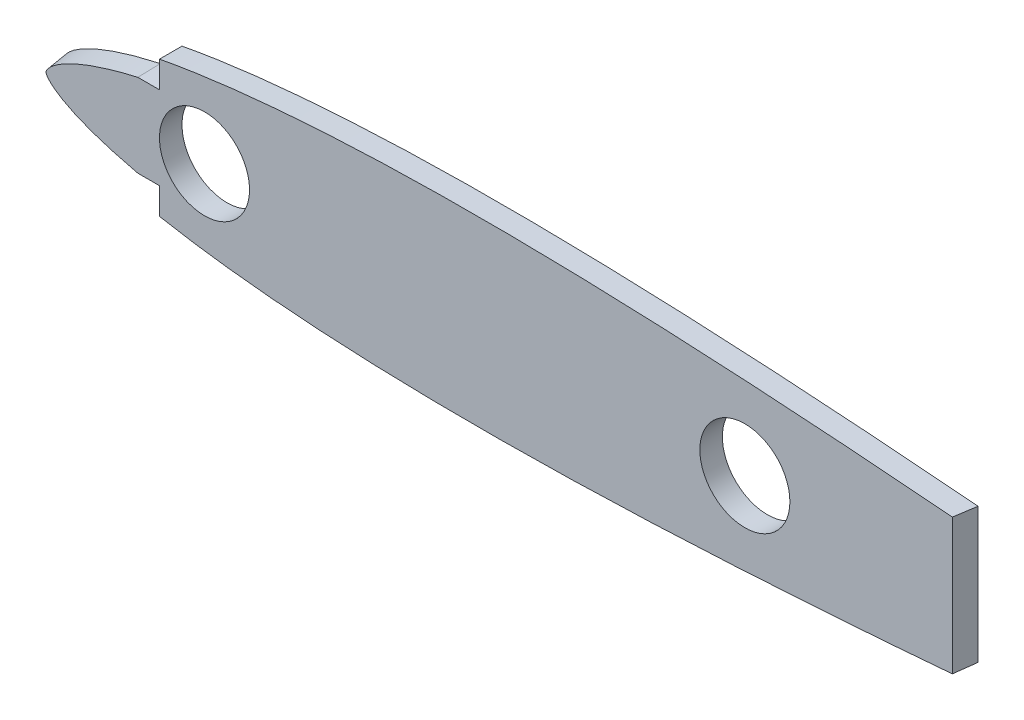
SolidWorks part; units mm, degrees
material "Balsa"
ref_plane "Front Plane" through (0, 0, 0) normal (0, 0, 1) x (1, 0, 0)
ref_plane "Top Plane" through (0, 0, 0) normal (0, 1, 0) x (1, 0, 0)
ref_plane "Right Plane" through (0, 0, 0) normal (1, 0, 0) x (0, 0, -1)
curve "Curve6"
  spline degree 3 poles (214.2507, -0.3619, 0) (214.2507, 0.3619, 0) (213.529, 0.2735, 0) (212.6145, 0.5309, 0) (210.9374, 0.6901, 0) (208.6782, 1.0315, 0) (205.7679, 1.4126, 0) (202.2583, 1.8823, 0) (198.1585, 2.4132, 0) (193.4982, 3.0043, 0) (188.3046, 3.6452, 0) (182.6103, 4.3273, 0) (176.4501, 5.042, 0) (169.8621, 5.7798, 0) (162.8869, 6.5315, 0) (155.5675, 7.2878, 0) (147.9491, 8.039, 0) (140.0787, 8.7745, 0) (132.0046, 9.4847, 0) (123.7769, 10.1577, 0) (115.4459, 10.7824, 0) (107.0633, 11.3474, 0) (98.6805, 11.8408, 0) (90.3493, 12.2502, 0) (82.1211, 12.5645, 0) (74.0464, 12.7737, 0) (66.175, 12.8673, 0) (58.5554, 12.8381, 0) (51.2345, 12.6804, 0) (44.2574, 12.3902, 0) (37.667, 11.9666, 0) (31.5038, 11.4111, 0) (25.8056, 10.7279, 0) (20.6071, 9.9229, 0) (15.9397, 9.0044, 0) (11.8309, 7.9828, 0) (8.304, 6.8681, 0) (5.3769, 5.6708, 0) (3.0589, 4.3988, 0) (1.3536, 3.0497, 0) (0.2614, 1.5908, 0) (-0.1218, 0, 0) (0.2614, -1.5908, 0) (1.3536, -3.0497, 0) (3.0589, -4.3988, 0) (5.3769, -5.6708, 0) (8.304, -6.8681, 0) (11.8309, -7.9828, 0) (15.9397, -9.0044, 0) (20.6071, -9.9229, 0) (25.8056, -10.7279, 0) (31.5038, -11.4111, 0) (37.667, -11.9666, 0) (44.2574, -12.3902, 0) (51.2345, -12.6804, 0) (58.5554, -12.8381, 0) (66.175, -12.8673, 0) (74.0464, -12.7737, 0) (82.1211, -12.5645, 0) (90.3493, -12.2502, 0) (98.6805, -11.8408, 0) (107.0633, -11.3474, 0) (115.4459, -10.7824, 0) (123.7769, -10.1577, 0) (132.0046, -9.4847, 0) (140.0787, -8.7745, 0) (147.9491, -8.039, 0) (155.5675, -7.2878, 0) (162.8869, -6.5315, 0) (169.8621, -5.7798, 0) (176.4501, -5.042, 0) (182.6103, -4.3273, 0) (188.3046, -3.6452, 0) (193.4982, -3.0043, 0) (198.1585, -2.4132, 0) (202.2583, -1.8823, 0) (205.7679, -1.4126, 0) (208.6782, -1.0315, 0) (210.9374, -0.6901, 0) (212.6145, -0.5309, 0) (213.529, -0.2735, 0) (214.2507, -0.3619, 0) (214.2507, 0.3619, 0) (213.529, 0.2735, 0) knots -0.004279 -0.001997 -0.001234 0 0.000762 0.003045 0.006832 0.012101 0.018818 0.026939 0.036415 0.047185 0.05918 0.072328 0.086544 0.101741 0.117823 0.134691 0.15224 0.170361 0.188941 0.207865 0.227016 0.246276 0.265525 0.284645 0.30352 0.322035 0.340078 0.357543 0.374325 0.39033 0.405464 0.419644 0.432793 0.444844 0.455738 0.465429 0.473886 0.481102 0.487102 0.491975 0.495931 0.499383 0.502835 0.50679 0.511664 0.517664 0.524879 0.533337 0.543028 0.553922 0.565972 0.579122 0.593302 0.608436 0.62444 0.641223 0.658687 0.676731 0.695245 0.714121 0.733241 0.75249 0.77175 0.7909 0.809825 0.828404 0.846525 0.864074 0.880942 0.897025 0.912222 0.926438 0.939585 0.951581 0.962351 0.971826 0.979948 0.986664 0.991933 0.995721 0.998003 0.998766 1 1.000762 1.003045 1.006832 periodic
sketch "Sketch1" plane through (0, 0, 0) normal (0, 0, 1) x (1, 0, 0)
  spline S0 degree 3 poles (214.2507, -0.3619) (214.2507, 0.3619) (213.529, 0.2735) (212.6145, 0.5309) (210.9374, 0.6901) (208.6782, 1.0315) (205.7679, 1.4126) (202.2583, 1.8823) (198.1585, 2.4132) (193.4982, 3.0043) (188.3046, 3.6452) (182.6103, 4.3273) (176.4501, 5.042) (169.8621, 5.7798) (162.8869, 6.5315) (155.5675, 7.2878) (147.9491, 8.039) (140.0787, 8.7745) (132.0046, 9.4847) (123.7769, 10.1577) (115.4459, 10.7824) (107.0633, 11.3474) (98.6805, 11.8408) (90.3493, 12.2502) (82.1211, 12.5645) (74.0464, 12.7737) (66.175, 12.8673) (58.5554, 12.8381) (51.2345, 12.6804) (44.2574, 12.3902) (37.667, 11.9666) (31.5038, 11.4111) (25.8056, 10.7279) (20.6071, 9.9229) (15.9397, 9.0044) (11.8309, 7.9828) (8.304, 6.8681) (5.3769, 5.6708) (3.0589, 4.3988) (1.3536, 3.0497) (0.2614, 1.5908) (-0.1218, 0) (0.2614, -1.5908) (1.3536, -3.0497) (3.0589, -4.3988) (5.3769, -5.6708) (8.304, -6.8681) (11.8309, -7.9828) (15.9397, -9.0044) (20.6071, -9.9229) (25.8056, -10.7279) (31.5038, -11.4111) (37.667, -11.9666) (44.2574, -12.3902) (51.2345, -12.6804) (58.5554, -12.8381) (66.175, -12.8673) (74.0464, -12.7737) (82.1211, -12.5645) (90.3493, -12.2502) (98.6805, -11.8408) (107.0633, -11.3474) (115.4459, -10.7824) (123.7769, -10.1577) (132.0046, -9.4847) (140.0787, -8.7745) (147.9491, -8.039) (155.5675, -7.2878) (162.8869, -6.5315) (169.8621, -5.7798) (176.4501, -5.042) (182.6103, -4.3273) (188.3046, -3.6452) (193.4982, -3.0043) (198.1585, -2.4132) (202.2583, -1.8823) (205.7679, -1.4126) (208.6782, -1.0315) (210.9374, -0.6901) (212.6145, -0.5309) (213.529, -0.2735) (214.2507, -0.3619) (214.2507, 0.3619) (213.529, 0.2735) knots -0.004279 -0.001997 -0.001234 0 0.000762 0.003045 0.006832 0.012101 0.018818 0.026939 0.036415 0.047185 0.05918 0.072328 0.086544 0.101741 0.117823 0.134691 0.15224 0.170361 0.188941 0.207865 0.227016 0.246276 0.265525 0.284645 0.30352 0.322035 0.340078 0.357543 0.374325 0.39033 0.405464 0.419644 0.432793 0.444844 0.455738 0.465429 0.473886 0.481102 0.487102 0.491975 0.495931 0.499383 0.502835 0.50679 0.511664 0.517664 0.524879 0.533337 0.543028 0.553922 0.565972 0.579122 0.593302 0.608436 0.62444 0.641223 0.658687 0.676731 0.695245 0.714121 0.733241 0.75249 0.77175 0.7909 0.809825 0.828404 0.846525 0.864074 0.880942 0.897025 0.912222 0.926438 0.939585 0.951581 0.962351 0.971826 0.979948 0.986664 0.991933 0.995721 0.998003 0.998766 1 1.000762 1.003045 1.006832 only from (214.122, 0.2698) to (214.122, 0.2698) construction
  spline S1 degree 3 poles (214.2507, -0.3619) (214.2507, 0.3619) (213.529, 0.2735) (212.6145, 0.5309) (210.9374, 0.6901) (208.6782, 1.0315) (205.7679, 1.4126) (202.2583, 1.8823) (198.1585, 2.4132) (193.4982, 3.0043) (188.3046, 3.6452) (182.6103, 4.3273) (176.4501, 5.042) (169.8621, 5.7798) (162.8869, 6.5315) (155.5675, 7.2878) (147.9491, 8.039) (140.0787, 8.7745) (132.0046, 9.4847) (123.7769, 10.1577) (115.4459, 10.7824) (107.0633, 11.3474) (98.6805, 11.8408) (90.3493, 12.2502) (82.1211, 12.5645) (74.0464, 12.7737) (66.175, 12.8673) (58.5554, 12.8381) (51.2345, 12.6804) (44.2574, 12.3902) (37.667, 11.9666) (31.5038, 11.4111) (25.8056, 10.7279) (20.6071, 9.9229) (15.9397, 9.0044) (11.8309, 7.9828) (8.304, 6.8681) (5.3769, 5.6708) (3.0589, 4.3988) (1.3536, 3.0497) (0.2614, 1.5908) (-0.1218, 0) (0.2614, -1.5908) (1.3536, -3.0497) (3.0589, -4.3988) (5.3769, -5.6708) (8.304, -6.8681) (11.8309, -7.9828) (15.9397, -9.0044) (20.6071, -9.9229) (25.8056, -10.7279) (31.5038, -11.4111) (37.667, -11.9666) (44.2574, -12.3902) (51.2345, -12.6804) (58.5554, -12.8381) (66.175, -12.8673) (74.0464, -12.7737) (82.1211, -12.5645) (90.3493, -12.2502) (98.6805, -11.8408) (107.0633, -11.3474) (115.4459, -10.7824) (123.7769, -10.1577) (132.0046, -9.4847) (140.0787, -8.7745) (147.9491, -8.039) (155.5675, -7.2878) (162.8869, -6.5315) (169.8621, -5.7798) (176.4501, -5.042) (182.6103, -4.3273) (188.3046, -3.6452) (193.4982, -3.0043) (198.1585, -2.4132) (202.2583, -1.8823) (205.7679, -1.4126) (208.6782, -1.0315) (210.9374, -0.6901) (212.6145, -0.5309) (213.529, -0.2735) (214.2507, -0.3619) (214.2507, 0.3619) (213.529, 0.2735) knots -0.004279 -0.001997 -0.001234 0 0.000762 0.003045 0.006832 0.012101 0.018818 0.026939 0.036415 0.047185 0.05918 0.072328 0.086544 0.101741 0.117823 0.134691 0.15224 0.170361 0.188941 0.207865 0.227016 0.246276 0.265525 0.284645 0.30352 0.322035 0.340078 0.357543 0.374325 0.39033 0.405464 0.419644 0.432793 0.444844 0.455738 0.465429 0.473886 0.481102 0.487102 0.491975 0.495931 0.499383 0.502835 0.50679 0.511664 0.517664 0.524879 0.533337 0.543028 0.553922 0.565972 0.579122 0.593302 0.608436 0.62444 0.641223 0.658687 0.676731 0.695245 0.714121 0.733241 0.75249 0.77175 0.7909 0.809825 0.828404 0.846525 0.864074 0.880942 0.897025 0.912222 0.926438 0.939585 0.951581 0.962351 0.971826 0.979948 0.986664 0.991933 0.995721 0.998003 0.998766 1 1.000762 1.003045 1.006832 only from (214.122, 0.2698) to (214.122, 0.2698)
extrude "Boss-Extrude1" add sketch "Sketch1" along normal blind 3.175
sketch "Sketch2" plane through (0, 0, 3.175) normal (0, 0, 1) x (1, 0, 0)
  circle A0 centre (25.4, 0) radius 6.35
  circle A1 centre (101.6, 0) radius 6.35
  dimension "D1" = 12.7
  dimension "D2" = 12.7
  dimension "D3" = 0
  dimension "D4" = 0
  dimension "D5" = 25.4
  dimension "D6" = 101.6
extrude "Cut-Extrude1" cut sketch "Sketch2" against normal through all
sketch "Sketch4" plane through (0, 0, 0) normal (0, 1, 0) x (1, 0, 0)
  line L2 (131.3014, 0) -> (130.8547, -3.175)
  line L4 (214.2185, 0) -> (0, 0) construction
  line L5 (214.2185, 0) -> (131.3014, 0)
  line L6 (214.2185, -3.175) -> (214.2185, 0) construction
  line L7 (214.2185, -3.175) -> (214.2185, 0)
  line L11 (130.8547, -3.175) -> (214.2185, -3.175)
extrude "Cut-Extrude2" cut sketch "Sketch4" against normal through all both and the other way through all contours L5 L2 L11 L7
sketch "Sketch5" plane through (0, 0, 0) normal (0, 0, -1) x (-1, 0, 0)
  line L0 (-19.05, -9.6949) -> (-19.05, -5.9522)
  line L1 (-19.05, -9.6949) -> (-19.05, -5.9522)
  line L2 (-16.002, -5.9522) -> (-19.05, -5.9522)
  line L3 (-16.002, -5.9522) -> (-19.05, -5.9522)
  line L4 (-19.05, 5.9522) -> (-19.05, 9.6949)
  line L5 (-19.05, 5.9522) -> (-19.05, 9.6949)
  line L6 (-19.05, 5.9522) -> (-16.002, 5.9522)
  line L7 (-19.05, 5.9522) -> (-16.002, 5.9522)
  line L8 (-19.05, 9.6949) -> (-19.05, 12.3776)
  line L9 (-19.05, 12.3776) -> (3.9372, 8.6357)
  line L10 (3.9372, 8.6357) -> (2.5117, -11.7446)
  line L11 (2.5117, -11.7446) -> (-19.05, -12.3014)
  line L12 (-19.05, -12.3014) -> (-19.05, -9.6949)
  spline S0 degree 3 poles (1979.4926, 138.2298) (-139.8627, -22.8717) (-64.1253, 18.5865) (-12.6489, 5.1346) (-11.5484, 4.8257) (-10.4651, 4.4981) (-9.3996, 4.1488) (-8.3537, 3.7753) (-7.5049, 3.4422) (-6.8429, 3.1616) (-6.1948, 2.871) (-5.4147, 2.488) (-4.6839, 2.0746) (-4.1514, 1.7348) (-3.7822, 1.4766) (-3.4495, 1.2179) (-3.1565, 0.9593) (-2.9074, 0.7021) (-2.7169, 0.4734) (-2.62, 0.3293) (-2.5683, 0.2322) (-2.5397, 0.1664) (-2.5186, 0.105) (-2.5054, 0.0553) (-2.4997, 0.023) (-2.4987, 0) (-2.4997, -0.023) (-2.5054, -0.0553) (-2.5186, -0.105) (-2.5397, -0.1664) (-2.5683, -0.2322) (-2.62, -0.3293) (-2.7169, -0.4734) (-2.9074, -0.7021) (-3.1565, -0.9593) (-3.4496, -1.2179) (-3.7821, -1.4766) (-4.1514, -1.7348) (-4.6837, -2.0745) (-5.4148, -2.4881) (-6.1948, -2.871) (-6.8429, -3.1616) (-7.5049, -3.4422) (-8.3537, -3.7753) (-9.3996, -4.1488) (-10.4651, -4.4981) (-11.5484, -4.8257) (-12.649, -5.1346) (-63.4171, -18.4015) (-138.5465, 21.5522) (1981.2096, -108.9254) knots -4.215654 -4.215654 -4.215654 -4.215654 0.0625 0.09375 0.125 0.15625 0.1875 0.21875 0.25 0.265625 0.28125 0.3125 0.34375 0.359375 0.375 0.390625 0.40625 0.421875 0.4375 0.453125 0.460938 0.46875 0.476562 0.484375 0.492188 0.5 0.507812 0.515625 0.523438 0.53125 0.539062 0.546875 0.5625 0.578125 0.59375 0.609375 0.625 0.640625 0.65625 0.6875 0.71875 0.734375 0.75 0.78125 0.8125 0.84375 0.875 0.90625 0.9375 5.15664 5.15664 5.15664 5.15664 only from (-16.002, 5.9522) to (-16.002, -5.9522)
  spline S1 degree 3 poles (-16.002, 5.9522) (-15.2548, 5.7866) (-14.1313, 5.522) (-12.6489, 5.1346) (-11.5484, 4.8257) (-10.4651, 4.4981) (-9.3996, 4.1488) (-8.3537, 3.7753) (-7.5049, 3.4422) (-6.8429, 3.1616) (-6.1948, 2.871) (-5.4147, 2.488) (-4.6839, 2.0746) (-4.1514, 1.7348) (-3.7822, 1.4766) (-3.4495, 1.2179) (-3.1565, 0.9593) (-2.9074, 0.7021) (-2.7169, 0.4734) (-2.62, 0.3293) (-2.5683, 0.2322) (-2.5397, 0.1664) (-2.5186, 0.105) (-2.5054, 0.0553) (-2.4997, 0.023) (-2.4987, 0) (-2.4997, -0.023) (-2.5054, -0.0553) (-2.5186, -0.105) (-2.5397, -0.1664) (-2.5683, -0.2322) (-2.62, -0.3293) (-2.7169, -0.4734) (-2.9074, -0.7021) (-3.1565, -0.9593) (-3.4496, -1.2179) (-3.7821, -1.4766) (-4.1514, -1.7348) (-4.6837, -2.0745) (-5.4148, -2.4881) (-6.1948, -2.871) (-6.8429, -3.1616) (-7.5049, -3.4422) (-8.3537, -3.7753) (-9.3996, -4.1488) (-10.4651, -4.4981) (-11.5484, -4.8257) (-12.649, -5.1346) (-14.1311, -5.5219) (-15.2548, -5.7866) (-16.002, -5.9522) knots 0 0 0 0 0.0625 0.09375 0.125 0.15625 0.1875 0.21875 0.25 0.265625 0.28125 0.3125 0.34375 0.359375 0.375 0.390625 0.40625 0.421875 0.4375 0.453125 0.460938 0.46875 0.476562 0.484375 0.492188 0.5 0.507812 0.515625 0.523438 0.53125 0.539062 0.546875 0.5625 0.578125 0.59375 0.609375 0.625 0.640625 0.65625 0.6875 0.71875 0.734375 0.75 0.78125 0.8125 0.84375 0.875 0.90625 0.9375 1 1 1 1
sketch "Sketch6" plane through (0, 0, 3.175) normal (0, 0, 1) x (1, 0, 0)
  line L0 (19.05, -5.8564) -> (19.05, -9.6045)
  line L1 (19.05, -5.8564) -> (19.05, -9.6045)
  line L2 (16.002, -5.8557) -> (19.05, -5.8564)
  line L3 (16.002, -5.8557) -> (19.05, -5.8564)
  line L4 (19.05, 9.6045) -> (19.05, 5.8564)
  line L5 (19.05, 9.6045) -> (19.05, 5.8564)
  line L6 (16.002, 5.8557) -> (19.05, 5.8564)
  line L7 (16.002, 5.8557) -> (19.05, 5.8564)
  line L8 (19.05, 9.6045) -> (19.05, 13.4998)
  line L9 (19.05, 13.4998) -> (-7.4002, 8.6709)
  line L10 (-7.4002, 8.6709) -> (-3.1768, -18.7418)
  line L11 (-3.1768, -18.7418) -> (19.05, -13.4967)
  line L12 (19.05, -13.4967) -> (19.05, -9.6045)
  spline S0 degree 3 poles (-1980.2608, 125.8125) (136.4057, -21.708) (62.4805, 18.4549) (12.7578, 5.0379) (11.6937, 4.7298) (10.6467, 4.4033) (9.6177, 4.0558) (8.6083, 3.6846) (7.6262, 3.2879) (6.6786, 2.8637) (5.7792, 2.4089) (5.0789, 2.0005) (4.5709, 1.6655) (4.2202, 1.4115) (3.9059, 1.1576) (3.6312, 0.9047) (3.3999, 0.6539) (3.2267, 0.4331) (3.1267, 0.2697) (3.0755, 0.1444) (3.0492, 0.0377) (3.0474, 0) (3.0492, -0.0377) (3.0755, -0.1444) (3.1267, -0.2697) (3.2267, -0.4331) (3.3999, -0.6539) (3.6312, -0.9046) (3.9059, -1.1577) (4.2201, -1.4115) (4.571, -1.6655) (5.0788, -2.0004) (5.7793, -2.409) (6.6785, -2.8637) (7.6262, -3.2879) (8.6083, -3.6846) (9.6177, -4.0558) (10.6467, -4.4033) (11.6936, -4.7298) (12.7579, -5.0379) (61.7896, -18.2686) (135.1259, 20.4118) (-1981.8383, -96.8635) knots -4.20929 -4.20929 -4.20929 -4.20929 0.0625 0.09375 0.125 0.15625 0.1875 0.21875 0.25 0.28125 0.3125 0.34375 0.359375 0.375 0.390625 0.40625 0.421875 0.4375 0.453125 0.46875 0.484375 0.5 0.515625 0.53125 0.546875 0.5625 0.578125 0.59375 0.609375 0.625 0.640625 0.65625 0.6875 0.71875 0.75 0.78125 0.8125 0.84375 0.875 0.90625 0.9375 5.149795 5.149795 5.149795 5.149795 only from (16.002, 5.8557) to (16.002, -5.8557)
  spline S1 degree 3 poles (16.002, 5.8557) (15.279, 5.6897) (14.1918, 5.4249) (12.7578, 5.0379) (11.6937, 4.7298) (10.6467, 4.4033) (9.6177, 4.0558) (8.6083, 3.6846) (7.6262, 3.2879) (6.6786, 2.8637) (5.7792, 2.4089) (5.0789, 2.0005) (4.5709, 1.6655) (4.2202, 1.4115) (3.9059, 1.1576) (3.6312, 0.9047) (3.3999, 0.6539) (3.2267, 0.4331) (3.1267, 0.2697) (3.0755, 0.1444) (3.0492, 0.0377) (3.0474, 0) (3.0492, -0.0377) (3.0755, -0.1444) (3.1267, -0.2697) (3.2267, -0.4331) (3.3999, -0.6539) (3.6312, -0.9046) (3.9059, -1.1577) (4.2201, -1.4115) (4.571, -1.6655) (5.0788, -2.0004) (5.7793, -2.409) (6.6785, -2.8637) (7.6262, -3.2879) (8.6083, -3.6846) (9.6177, -4.0558) (10.6467, -4.4033) (11.6936, -4.7298) (12.7579, -5.0379) (14.1916, -5.4248) (15.279, -5.6897) (16.002, -5.8557) knots 0 0 0 0 0.0625 0.09375 0.125 0.15625 0.1875 0.21875 0.25 0.28125 0.3125 0.34375 0.359375 0.375 0.390625 0.40625 0.421875 0.4375 0.453125 0.46875 0.484375 0.5 0.515625 0.53125 0.546875 0.5625 0.578125 0.59375 0.609375 0.625 0.640625 0.65625 0.6875 0.71875 0.75 0.78125 0.8125 0.84375 0.875 0.90625 0.9375 1 1 1 1
loft "Cut-Loft1" cut profiles "Sketch6", "Sketch5"
